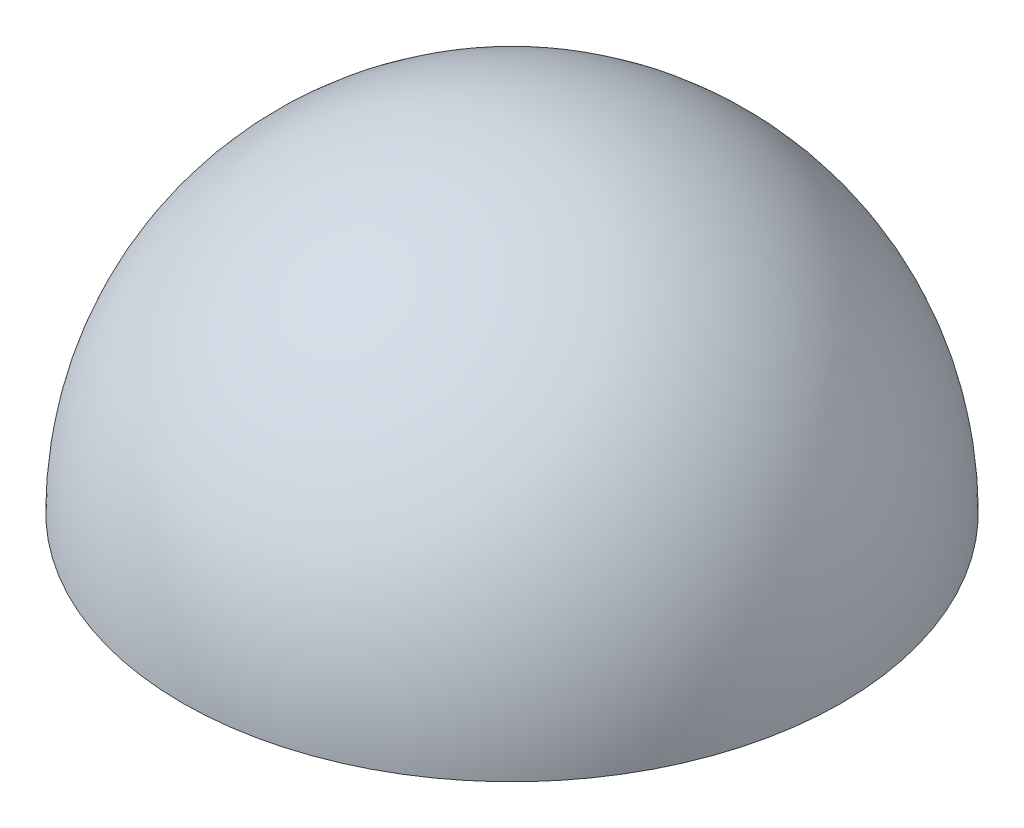
SolidWorks part; units mm, degrees
ref_plane "前视基准面" through (0, 0, 0) normal (0, 0, 1) x (1, 0, 0)
ref_plane "上视基准面" through (0, 0, 0) normal (0, 1, 0) x (1, 0, 0)
ref_plane "右视基准面" through (0, 0, 0) normal (1, 0, 0) x (0, 0, -1)
other "Configuration Table"
sketch "草图1" plane through (0, 0, 0) normal (0, 0, 1) x (1, 0, 0)
  line L0 (0, 0) -> (-70, 0)
  line L1 (0, 0) -> (0, 70)
  arc A0 (-70, 0) -> (0, 70) centre (0, 0) cw
  point P5 (0, 0)
  dimension "D1" = 70
revolve "旋转1" add sketch "草图1" angle 360 about L1
